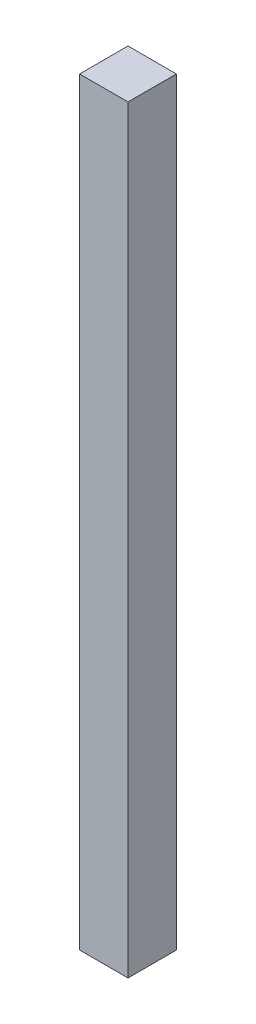
SolidWorks part; units mm, degrees
ref_plane "Front Plane" through (0, 0, 0) normal (0, 0, 1) x (1, 0, 0)
ref_plane "Top Plane" through (0, 0, 0) normal (0, 1, 0) x (1, 0, 0)
ref_plane "Right Plane" through (0, 0, 0) normal (1, 0, 0) x (0, 0, -1)
sketch "Sketch1" plane through (0, 0, 0) normal (0, 0, 1) x (1, 0, 0)
  line L0 (685.8, -635) -> (0, -635) construction
  line L1 (685.8, -38.1) -> (647.7, -38.1)
  line L2 (685.8, -38.1) -> (685.8, -635)
  line L3 (685.8, -635) -> (647.7, -635)
  line L4 (647.7, -38.1) -> (647.7, -635)
extrude "Boss-Extrude1" add sketch "Sketch1" along normal up to vertex (38.1 mm away) contours L4 L3 L2 L1
